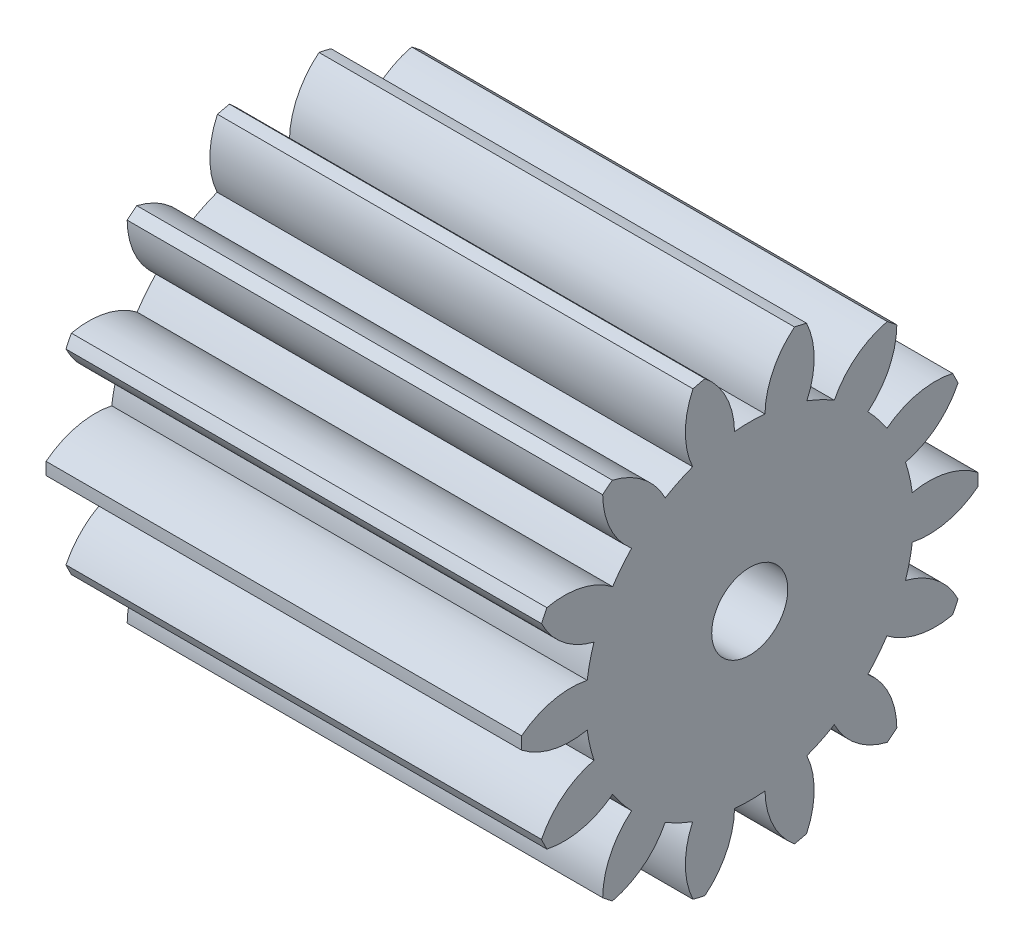
SolidWorks part; units mm, degrees
ref_plane "Plane1" through (0, 0, 0) normal (0, 0, 1) x (1, 0, 0)
ref_plane "Plane2" through (0, 0, 0) normal (0, 1, 0) x (1, 0, 0)
ref_plane "Plane3" through (0, 0, 0) normal (1, 0, 0) x (0, 0, -1)
sketch "HoldingSke" plane through (0, 0, 0) normal (0, 1, 0) x (1, 0, 0)
  line L0 (0, 0) -> (3.2343, -0.8064)
  line L1 (-15, 0) -> (100, 0) construction
  line L2 (0, 0) -> (-2.1039, 2.3779)
  line L3 (0, 0) -> (-11.863, 4.5341)
  line L4 (0, 0) -> (8.3795, 2.0892)
  line L5 (0, 0) -> (-46.8476, -17.4728)
  line L6 (0, 0) -> (-4.1448, -2.7965)
  line L7 (-2.1039, 2.3779) -> (8.6586, 51.2059)
  line L8 (-76.2, 54.61) -> (-76.1, 54.61)
  line L9 (-71.009, 38.7566) -> (-53.1078, 45.2721)
  line L10 (-76.2, 71.12) -> (104.1128, 71.12)
  line L11 (0, 0) -> (-5, 0)
  line L12 (-76.2, 101.6) -> (-76.19, 101.6)
  line L13 (24.9733, 27.94) -> (52.9518, 28.4284)
  line L14 (24.9733, 27.94) -> (24.9743, 27.94)
  line L15 (24.9733, 27.94) -> (100.4006, 29.5858)
  line L16 (-63.627, -0.3) -> (-12.827, -0.3)
  circle A0 centre (0, 0) radius 0.4
  circle A1 centre (0, 0) radius 1.724
  circle A2 centre (0, 0) radius 37.5
  circle A3 centre (0, 0) radius 0.4
  dimension "MHD" = 3.448
  dimension "Hub_dia" = 75
  dimension "Bore" = 0.8
  dimension "MBD" = 0.8
  dimension "Num_teeth" = 14
  dimension "Pitch" = 3.3333
  dimension "Overall_len" = 50
  dimension "Show_teeth" = 14
  dimension "Thickness" = 5
  dimension "OAL" = 50.0001
  dimension "T_dim" = 0.1
  dimension "Ap" = 20
  dimension "H" = 19.05
  dimension "Pitch_radius" = 180.3128
  dimension "Width" = 5
  dimension "Backlash" = 0.01
  dimension "Addendum_fac" = 1
  dimension "Dedendum_fac" = 1.25
  dimension "Clearance_fac" = 0.25
  dimension "Dedendum_add" = 0.001
  dimension "Module" = 0.3
sketch "BasProSke" plane through (0, 0, 0) normal (0, 1, 0) x (1, 0, 0)
  line L0 (-10, 0) -> (60, 0) construction
  line L1 (0, 0) -> (0, 2.4)
  line L2 (0, 0) -> (5, 0)
  line L3 (5, 0) -> (5, 2.4)
  line L4 (5, 2.4) -> (0, 2.4)
  dimension "Thickness" = 5
  dimension "Diameter" = 4.8
revolve "Base-Revolve" add sketch "BasProSke" angle 360 about L0
sketch "TooCutSke" plane through (0, 0, 0) normal (1, 0, 0) x (0, 0, -1)
  line L1 (0, 0) -> (0, 107) construction
  line L2 (0, 0) -> (-0.2526, 2.0848) construction
  line L3 (0, 0) -> (-0.9296, 4.0727) construction
  line L4 (-0.2526, 2.0848) -> (-0.4648, 2.0363) construction
  arc A0 (0.1601, 1.7166) -> (-0.1601, 1.7166) centre (0, 0) ccw
  arc A1 (0.4969, 2.374) -> (-0.4969, 2.374) centre (0, 0) ccw
  circle A2 centre (0, 0) radius 2.1 construction
  circle A3 centre (0, 0) radius 1.9734 construction
  arc A4 (-0.1601, 1.7166) -> (-0.4969, 2.374) centre (-1, 1.7012) ccw
  arc A5 (0.4969, 2.374) -> (0.1601, 1.7166) centre (1, 1.7012) ccw
  dimension "Root_dia" = 3.448
  dimension "Overcut_dia" = 4.8508
  dimension "Pitch_dia" = 4.2
  dimension "Base_dia" = 3.9467
  dimension "Flank_rad" = 0.84
  dimension "Half_ang" = 12.857
  dimension "Half_CT" = 0.2176
extrude "ToothCut" cut sketch "TooCutSke" along normal through all
fillet "Breaks" [suppressed] radius 0.006
fillet "RootFillets" [suppressed] radius 0.076
pattern_circular "TeethCuts" count 14 every 25.714 about axis through (-10, 0, 0) along (1, 0, 0) of "ToothCut", "RootFillets", "Breaks"
sketch "HubNeaOneSke" plane through (0, 0, 0) normal (-1, 0, 0) x (0, 0, 1)
  circle A0 centre (0, 0) radius 1.724
  dimension "Diameter" = 3.448
extrude "HubNearOne" [suppressed] add sketch "HubNeaOneSke" along normal blind 45.0001
sketch "HubNeaBotSke" plane through (0, 0, 0) normal (-1, 0, 0) x (0, 0, 1)
  circle A0 centre (0, 0) radius 1.724
  dimension "Diameter" = 3.448
extrude "HubNearBoth" [suppressed] add sketch "HubNeaBotSke" along normal blind 22.5
ref_plane "FarPln" through (5, 0, 0) normal (1, 0, 0) x (0, 0, -1)
sketch "HubFarSke" plane through (5, 0, 0) normal (1, 0, 0) x (0, 0, -1)
  circle A0 centre (0, 0) radius 1.724
  dimension "Diameter" = 3.448
extrude "HubFar" [suppressed] add sketch "HubFarSke" along normal blind 22.5
sketch "BorSke" plane through (0, 0, 0) normal (1, 0, 0) x (0, 0, -1)
  circle A0 centre (0, 0) radius 0.4
  dimension "Diameter" = 0.8
extrude "Bore" cut sketch "BorSke" along normal mid plane 100.0001
sketch "KeySke" plane through (0, 0, 0) normal (1, 0, 0) x (0, 0, -1)
  line L0 (-0.05, 0) -> (-0.05, 0.5)
  line L1 (-0.05, 0.5) -> (0.05, 0.5)
  line L2 (0.05, 0.5) -> (0.05, 0)
  line L3 (0, 0) -> (0, 34) construction
  line L4 (-0.05, 0) -> (0.05, 0)
  dimension "Offset" = 0.5
  dimension "Width" = 0.1
extrude "Keyway" [suppressed] cut sketch "KeySke" along normal mid plane 100.0001
pattern_circular "Keyway2" [suppressed] count 2 every 90 about axis through (-10, 0, 0) along (1, 0, 0)
equation "' \"Module@HoldingSke\" = 6.35"
equation "' \"Num_teeth@HoldingSke\" = 12"
equation "' \"Ap@HoldingSke\" =  20"
equation "' \"Ap@HoldingSke\" = 20"
equation "' \"Width@HoldingSke\" = 0.5 * 25.4"
equation "' \"Hub_dia@HoldingSke\"= 1 * 25.4"
equation "' \"Hub_dia@HoldingSke\" = 1 * 25.4"
equation "' \"Overall_len@HoldingSke\" = 1.0 * 25.4"
equation "' \"Bore@HoldingSke\" = 0.75 * 25.4"
equation "' \"T_dim@HoldingSke\" = 0.1 * 25.4"
equation "' \"Width@KeySke\" = 0.25 * 25.4"
equation "' \"Show_teeth@HoldingSke\" = 13"
equation "' \"Backlash@HoldingSke\" = 0.009 * 25.4"
equation "' \"Addendum_fac@HoldingSke\" = 1.0"
equation "' \"Dedendum_fac@HoldingSke\" = 1.25"
equation "' \"Dedendum_add@HoldingSke\" = 0.00005 * 25.4"
equation "' \"Clearance_fac@HoldingSke\" = 0.25"
equation "\"Pitch@HoldingSke\" = 1 / \"Module@HoldingSke\""
equation "\"Overcut_dia@TooCutSke\" = (\"Num_teeth@HoldingSke\" + 2 * \"Addendum_fac@HoldingSke\") / \"Pitch@HoldingSke\" + 0.002 * 25.4"
equation "\"Pitch_dia@TooCutSke\" = \"Num_teeth@HoldingSke\" / \"Pitch@HoldingSke\""
equation "\"Base_dia@TooCutSke\" = \"Num_teeth@HoldingSke\" / \"Pitch@HoldingSke\" * cos((\"Ap@HoldingSke\"  * 3.14159265 / 180))"
equation "\"Root_dia@TooCutSke\" = (\"Num_teeth@HoldingSke\" + 2) / \"Pitch@HoldingSke\" - 2 * (\"Addendum_fac@HoldingSke\" + \"Dedendum_fac@HoldingSke\") / \"Pitch@HoldingSke\" - \"Dedendum_add@HoldingSke\" * 2"
equation "\"Half_ang@TooCutSke\" = 180 / \"Num_teeth@HoldingSke\""
equation "\"Half_CT@TooCutSke\" = \"Num_teeth@HoldingSke\" / \"Pitch@HoldingSke\" * sin((3.14159265 / 2 / \"Num_teeth@HoldingSke\")) / 2 - 7 * \"Backlash@HoldingSke\" / 4"
equation "\"Flank_rad@TooCutSke\" = \"Num_teeth@HoldingSke\" / \"Pitch@HoldingSke\" / 5"
equation "\"Radius@RootFillets\" = \"Clearance_fac@HoldingSke\" / \"Pitch@HoldingSke\" + \"Dedendum_add@HoldingSke\""
equation "\"Break_rad@Breaks\" = 0.02 / \"Pitch@HoldingSke\""
equation "\"Thickness@HoldingSke\" = \"Width@HoldingSke\""
equation "\"OAL@HoldingSke\" = \"Thickness@HoldingSke\""
equation "\"MHD@HoldingSke\" = (\"Num_teeth@HoldingSke\" + 2) / \"Pitch@HoldingSke\" - 2 * (\"Addendum_fac@HoldingSke\" + \"Dedendum_fac@HoldingSke\")  / \"Pitch@HoldingSke\" - \"Dedendum_add@HoldingSke\" * 2"
equation "\"MBD@HoldingSke\" = (\"Num_teeth@HoldingSke\" + 2) / \"Pitch@HoldingSke\" - 2 * (\"Addendum_fac@HoldingSke\" + \"Dedendum_fac@HoldingSke\")  / \"Pitch@HoldingSke\" - \"Dedendum_add@HoldingSke\" * 2 - 0.002 * 25.4"
equation "\"MHD@HoldingSke\" = ((sgn( \"MHD@HoldingSke\" - \"Hub_dia@HoldingSke\" )-1)*( \"MHD@HoldingSke\" - \"Hub_dia@HoldingSke\" ))/-2+ \"Hub_dia@HoldingSke\""
equation "\"MBD@HoldingSke\" = ((sgn( \"MBD@HoldingSke\" - \"Bore@HoldingSke\" )-1)*( \"MBD@HoldingSke\" - \"Bore@HoldingSke\" ))/-2+ \"Bore@HoldingSke\""
equation "\"OAL@HoldingSke\" = ((sgn( \"OAL@HoldingSke\" - \"Overall_len@HoldingSke\" )+1)*( \"OAL@HoldingSke\" - \"Overall_len@HoldingSke\" ))/2 + \"Overall_len@HoldingSke\" + 0.000002 * 25.4"
equation "\"Num_teeth@TeethCuts\" = int( \"Show_teeth@HoldingSke\" ) + 1"
equation "\"Num_teeth@TeethCuts\" = ((sgn( \"Num_teeth@TeethCuts\" - \"Num_teeth@HoldingSke\" )-1)*( \"Num_teeth@TeethCuts\" - \"Num_teeth@HoldingSke\" ))/-2+ \"Num_teeth@HoldingSke\""
equation "\"Num_teeth@TeethCuts\" = ((sgn( \"Num_teeth@TeethCuts\" - 2.0)+1)*( \"Num_teeth@TeethCuts\" - 2.0))/2 +2.0"
equation "\"Angle@TeethCuts\" = 360.0 / \"Num_teeth@HoldingSke\""
equation "\"Diameter@BasProSke\" = (\"Num_teeth@HoldingSke\" + 2 * \"Addendum_fac@HoldingSke\") / \"Pitch@HoldingSke\""
equation "\"Thickness@BasProSke\"  = \"Thickness@HoldingSke\""
equation "' \"Fillet_rad@BasProSke\" =  \"Thickness@HoldingSke\" * 0.05"
equation "' \"Fillet_rad@BasProSke\" = \"Thickness@HoldingSke\" * 0.05"
equation "\"MHD@HoldingSke\" = ((sgn( \"MHD@HoldingSke\" - \"Root_dia@TooCutSke\" )-1)*( \"MHD@HoldingSke\" - \"Root_dia@TooCutSke\" ))/-2+ \"Root_dia@TooCutSke\""
equation "\"Diameter@HubNeaOneSke\" = \"MHD@HoldingSke\""
equation "\"Length@HubNearOne\" = \"OAL@HoldingSke\" - \"Thickness@BasProSke\""
equation "\"Diameter@HubNeaBotSke\" = \"MHD@HoldingSke\""
equation "\"Length@HubNearBoth\" = ( \"OAL@HoldingSke\" - \"Thickness@BasProSke\" ) / 2.0"
equation "\"Thickness@FarPln\" = \"Thickness@BasProSke\""
equation "\"Diameter@HubFarSke\" = \"MHD@HoldingSke\""
equation "\"Length@HubFar\" = ( \"OAL@HoldingSke\" - \"Thickness@BasProSke\" ) / 2.0"
equation "\"Diameter@BorSke\" = \"MBD@HoldingSke\""
equation "\"D1@Bore\" = \"OAL@HoldingSke\" * 2.0"
equation "\"D1@Keyway\" = \"OAL@HoldingSke\" * 2.0"
equation "\"Offset@KeySke\" = \"T_dim@HoldingSke\" + \"MBD@HoldingSke\" / 2.0"
